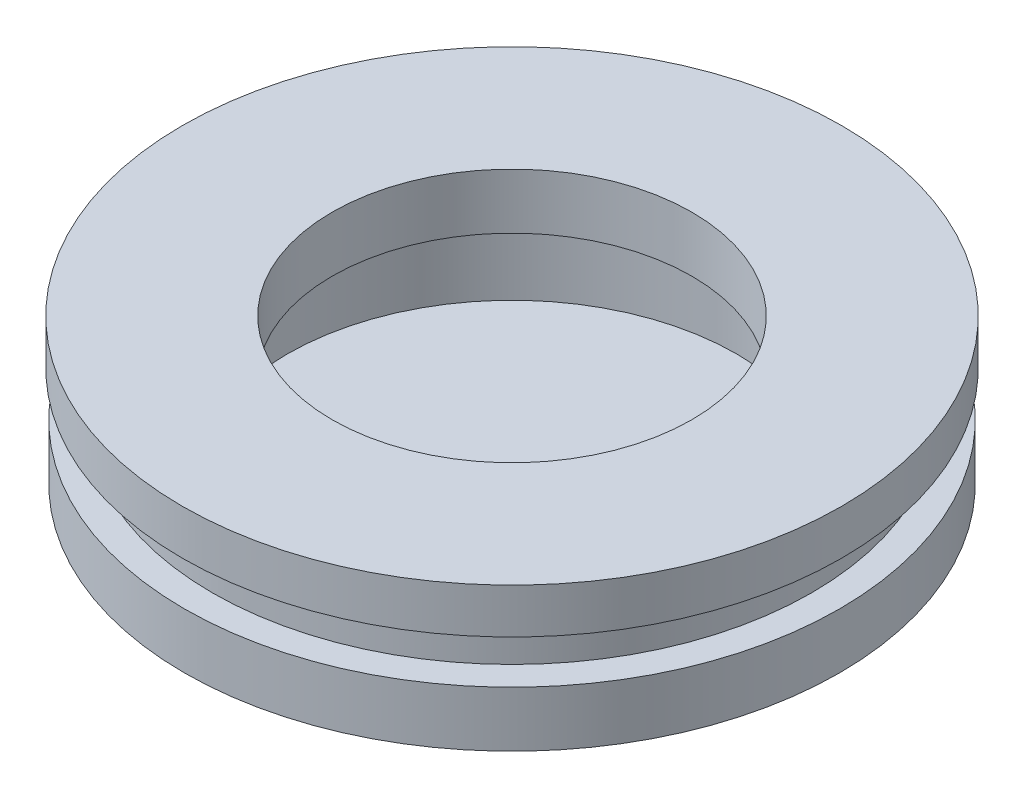
SolidWorks part; units mm, degrees
ref_plane "Front Plane" through (0, 0, 0) normal (0, 0, 1) x (1, 0, 0)
ref_plane "Top Plane" through (0, 0, 0) normal (0, 1, 0) x (1, 0, 0)
ref_plane "Right Plane" through (0, 0, 0) normal (1, 0, 0) x (0, 0, -1)
sketch "Sketch1" plane through (0, 0, 0) normal (0, 0, 1) x (1, 0, 0)
  line L0 (0, 0) -> (0, 8.828)
  line L1 (0, 8.828) -> (-11, 8.828)
  line L2 (-11, 8.828) -> (-11, 7.328)
  line L3 (-11, 7.328) -> (-10, 7.328)
  line L4 (-10, 7.328) -> (-10, 5.828)
  line L5 (-10, 5.828) -> (-10.9295, 5.828)
  line L6 (-10.9295, 5.828) -> (-10.9295, 3.978)
  line L7 (-10.9295, 3.978) -> (0, 0)
  point P8 (-10, 6.578)
  dimension "D1" = 1.5
  dimension "D2" = 1.5
  dimension "D3" = 1.85
  dimension "D4" = 11
  dimension "D5" = 10
  dimension "D6" = 20
revolve "Revolve1" add sketch "Sketch1" angle 360 about L0
sketch "Sketch2" plane through (0, 0, 0) normal (0, 0, 1) x (1, 0, 0)
  line L0 (0, 3.978) -> (0, 9.978)
  line L1 (10.9295, 3.978) -> (-10.9295, 3.978) construction
  line L2 (0, 9.978) -> (-6, 9.978)
  line L3 (-6, 9.978) -> (-6, 6.978)
  line L4 (-6, 6.978) -> (-7.5, 6.978)
  line L5 (-7.5, 6.978) -> (-7.5, 3.978)
  line L6 (-7.5, 3.978) -> (0, 3.978)
  dimension "D1" = 6
  dimension "D2" = 7.5
  dimension "D3" = 3
  dimension "D4" = 3
revolve "Cut-Revolve1" cut sketch "Sketch2" angle 360 about L0
